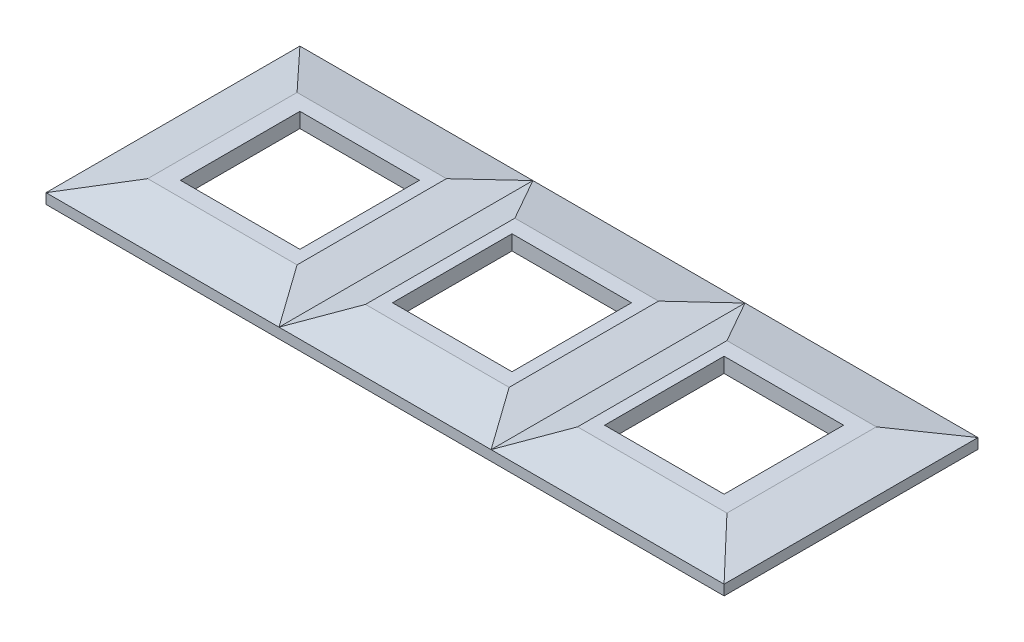
SolidWorks part; units mm, degrees
ref_plane "Спереди" through (0, 0, 0) normal (0, 0, 1) x (1, 0, 0)
ref_plane "Сверху" through (0, 0, 0) normal (0, 1, 0) x (1, 0, 0)
ref_plane "Справа" through (0, 0, 0) normal (1, 0, 0) x (0, 0, -1)
sketch "Эскиз1" plane through (0, 0, 0) normal (0, 0, 1) x (1, 0, 0)
  line L1 (-113.5, 0) -> (-113.5, 3.421)
  line L2 (-113.5, 3.421) -> (-96.9538, 7)
  line L3 (-96.9538, 7) -> (-46.9538, 7)
  line L4 (-113.5, 0) -> (113.5, 0)
  line L6 (0, 40.9923) -> (0, -28.3407) construction
  line L9 (-35.5, 3.421) -> (-24.0462, 7)
  line L11 (-35.5, 3.421) -> (-46.9538, 7)
  line L12 (35.5, 3.421) -> (46.9538, 7)
  line L13 (-24.0462, 7) -> (24.0462, 7)
  line L14 (35.5, 3.421) -> (24.0462, 7)
  line L17 (96.9538, 7) -> (46.9538, 7)
  line L23 (113.5, 3.421) -> (96.9538, 7)
  line L24 (113.5, 0) -> (113.5, 3.421)
  point P0 (-1.75, 0)
  point P8 (0, 7)
  point P15 (1.75, 0)
  point P16 (0, 7)
  point P17 (0, 0)
  point P19 (0, 0)
  point P21 (0, 7)
  point P22 (0, 0)
  point P23 (0, 0)
  point P24 (0, 0)
  point P25 (0, 0)
extrude "Бобышка-Вытянуть1" add sketch "Эскиз1" along normal mid plane 85
sketch "Эскиз2" plane through (0, 0, 0) normal (1, 0, 0) x (0, 0, -1)
  line L6 (0, 24.25) -> (0, -8.715) construction
  line L22 (42.5, 0) -> (-42.5, 0)
  line L23 (-42.5, 3.421) -> (-25, 7)
  line L24 (-42.5, 7) -> (42.5, 7) construction
  line L25 (-25, 7) -> (25, 7)
  line L26 (-42.5, 0) -> (-42.5, 3.421)
  line L27 (42.5, 0) -> (42.5, 3.421)
  line L28 (42.5, 3.421) -> (25, 7)
  point P10 (0, 0)
  point P13 (0, 7)
extrude "Вырез-Вытянуть1" cut sketch "Эскиз2" against normal mid plane 246 flip side to cut
sketch "Эскиз3" plane through (0, 0, 0) normal (0, -1, 0) x (1, 0, 0)
  line L0 (51, 20) -> (91, 20)
  line L1 (-20, 20) -> (20, 20)
  line L2 (-20, 20) -> (-20, -20)
  line L3 (-20, -20) -> (20, -20)
  line L4 (20, 20) -> (20, -20)
  line L5 (-20, 20) -> (20, -20) construction
  line L6 (-20, -20) -> (20, 20) construction
  line L7 (51, 20) -> (51, -20)
  line L8 (51, -20) -> (91, -20)
  line L13 (91, 20) -> (91, -20)
  line L14 (51, 20) -> (91, -20) construction
  line L15 (51, -20) -> (91, 20) construction
  line L16 (-91, 20) -> (-51, 20)
  line L17 (-91, 20) -> (-91, -20)
  line L18 (-91, -20) -> (-51, -20)
  line L19 (-51, 20) -> (-51, -20)
  line L20 (-91, 20) -> (-51, -20) construction
  line L21 (-91, -20) -> (-51, 20) construction
  point P0 (0, 0)
  point P5 (71, 0)
  point P6 (0, 0)
  point P8 (0, 0)
  point P12 (0, 0)
  point P14 (-71, 0)
  dimension "D1" = 2
  dimension "D2" = 2
extrude "Вырез-Вытянуть2" cut sketch "Эскиз3" against normal through all
sketch "Эскиз4" plane through (0, 0, 0) normal (0, -1, 0) x (1, 0, 0)
  line L1 (-111.5, 41) -> (111.5, 41)
  line L2 (-111.5, 41) -> (-111.5, -41)
  line L3 (-111.5, -41) -> (111.5, -41)
  line L4 (111.5, 41) -> (111.5, -41)
  line L5 (-111.5, 41) -> (111.5, -41) construction
  line L6 (-111.5, -41) -> (111.5, 41) construction
  point P0 (0, 0)
extrude "Вырез-Вытянуть3" cut sketch "Эскиз4" against normal blind 1
sketch "Эскиз5" plane through (0, 1, 0) normal (0, -1, 0) x (1, 0, 0)
  line L1 (-106.5, 35.5) -> (106.5, 35.5)
  line L2 (-106.5, 35.5) -> (-106.5, -35.5)
  line L3 (-106.5, -35.5) -> (106.5, -35.5)
  line L4 (106.5, 35.5) -> (106.5, -35.5)
  line L5 (-106.5, 35.5) -> (106.5, -35.5) construction
  line L6 (-106.5, -35.5) -> (106.5, 35.5) construction
  point P0 (0, 0)
extrude "Вырез-Вытянуть4" cut sketch "Эскиз5" against normal blind 1
